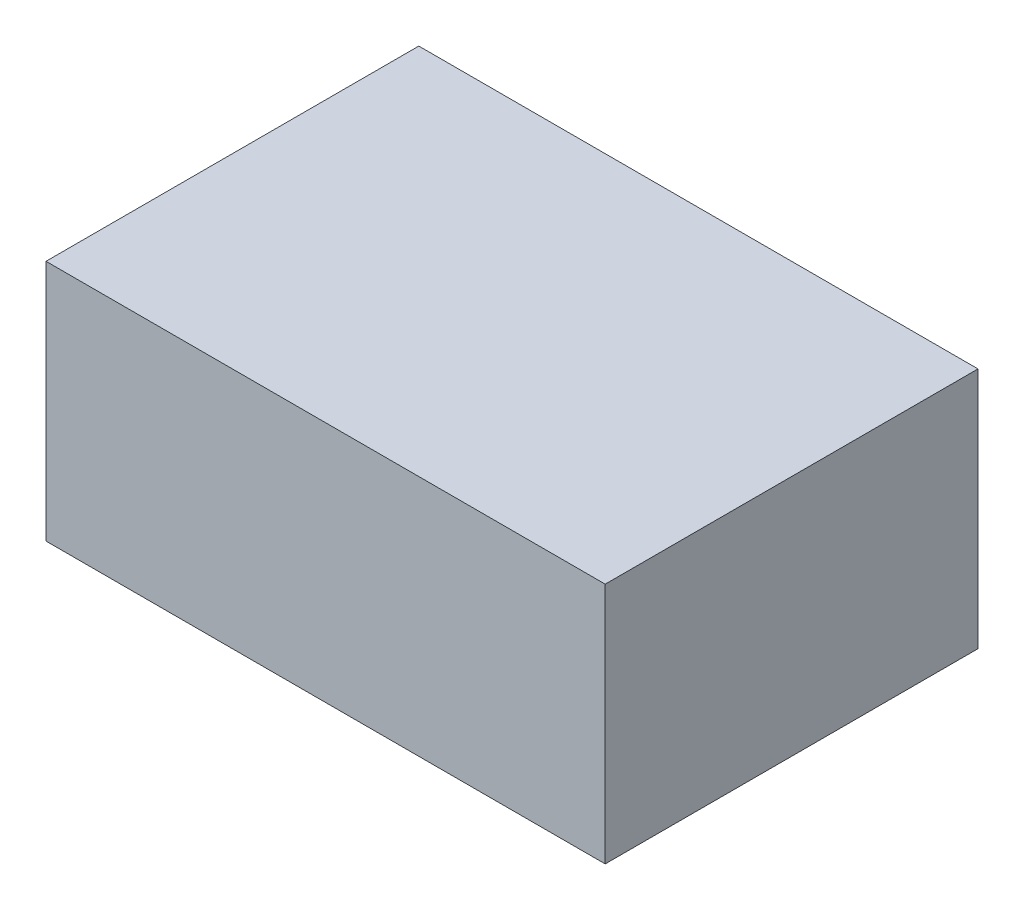
SolidWorks part; units mm, degrees
material "CA"
ref_plane "Front Plane" through (0, 0, 0) normal (0, 0, 1) x (1, 0, 0)
ref_plane "Top Plane" through (0, 0, 0) normal (0, 1, 0) x (1, 0, 0)
ref_plane "Right Plane" through (0, 0, 0) normal (1, 0, 0) x (0, 0, -1)
sketch "Sketch1" plane through (0, 0, 0) normal (0, 1, 0) x (1, 0, 0)
  line L1 (-229.1339, 172.4409) -> (70.8661, 172.4409)
  line L2 (-229.1339, 172.4409) -> (-229.1339, -27.5591)
  line L3 (-229.1339, -27.5591) -> (70.8661, -27.5591)
  line L4 (70.8661, 172.4409) -> (70.8661, -27.5591)
  dimension "D1" = 300
  dimension "D2" = 200
extrude "Boss-Extrude1" add sketch "Sketch1" along normal blind 130
